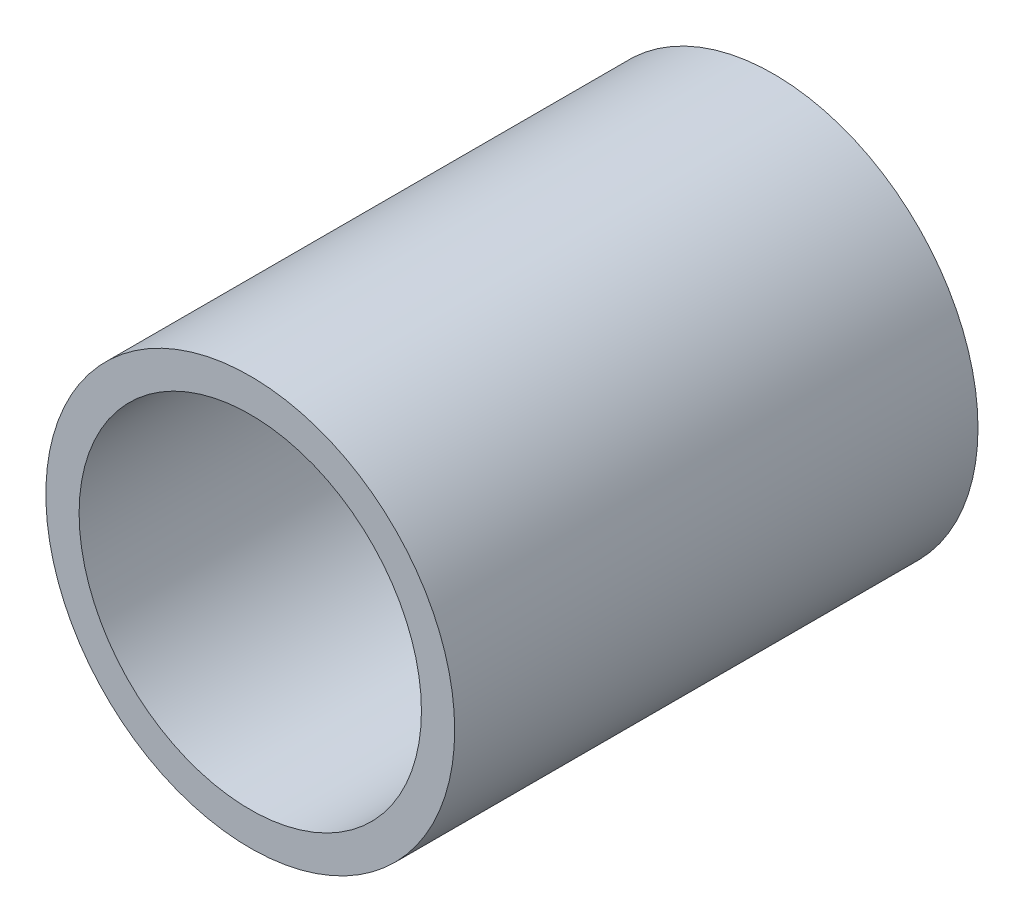
SolidWorks part; units mm, degrees
material "Leaded Commercial Bronze"
ref_plane "Front Plane" through (0, 0, 0) normal (0, 0, 1) x (1, 0, 0)
ref_plane "Top Plane" through (0, 0, 0) normal (0, 1, 0) x (1, 0, 0)
ref_plane "Right Plane" through (0, 0, 0) normal (1, 0, 0) x (0, 0, -1)
sketch "Sketch1" plane through (0, 0, 0) normal (0, 0, 1) x (1, 0, 0)
  circle A0 centre (-12.603, 4.5686) radius 4.7625
  circle A1 centre (-12.603, 4.5686) radius 3.9878
  dimension "D1" = 9.525
extrude "Extrude1" add sketch "Sketch1" along normal blind 12.192
